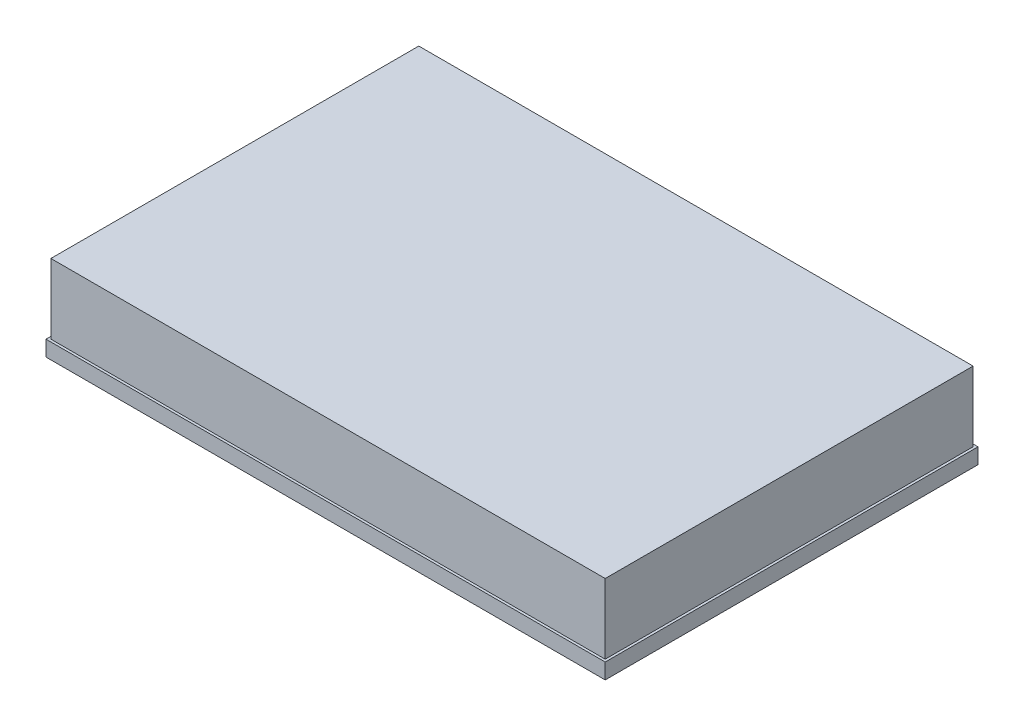
SolidWorks part; units mm, degrees
ref_plane "Front Plane" through (0, 0, 0) normal (0, 0, 1) x (1, 0, 0)
ref_plane "Top Plane" through (0, 0, 0) normal (0, 1, 0) x (1, 0, 0)
ref_plane "Right Plane" through (0, 0, 0) normal (1, 0, 0) x (0, 0, -1)
sketch "Sketch1" plane through (0, 0, 0) normal (0, 1, 0) x (1, 0, 0)
  line L1 (0, 0) -> (-114.3, 0)
  line L2 (0, 0) -> (0, 76.2)
  line L3 (0, 76.2) -> (-114.3, 76.2)
  line L4 (-114.3, 0) -> (-114.3, 76.2)
  dimension "D1" = 114.3
  dimension "D2" = 76.2
extrude "Boss-Extrude1" add sketch "Sketch1" along normal blind 3.175
sketch "Sketch3" plane through (0, 3.175, 0) normal (0, 1, 0) x (1, 0, 0)
  line L0 (-0.5, 75.7) -> (-113.8, 75.7)
  line L1 (-113.8, 75.7) -> (-113.8, 0.5)
  line L2 (-113.8, 0.5) -> (-0.5, 0.5)
  line L3 (-0.5, 0.5) -> (-0.5, 14.0347)
  line L4 (-0.5, 14.0347) -> (-0.5, 75.7)
  line L7 (-114.3, 76.2) -> (-114.3, 0) construction
  dimension "D1" = 113.3
  dimension "D2" = 0.5
extrude "Boss-Extrude4" add sketch "Sketch3" along normal blind 14.2875
